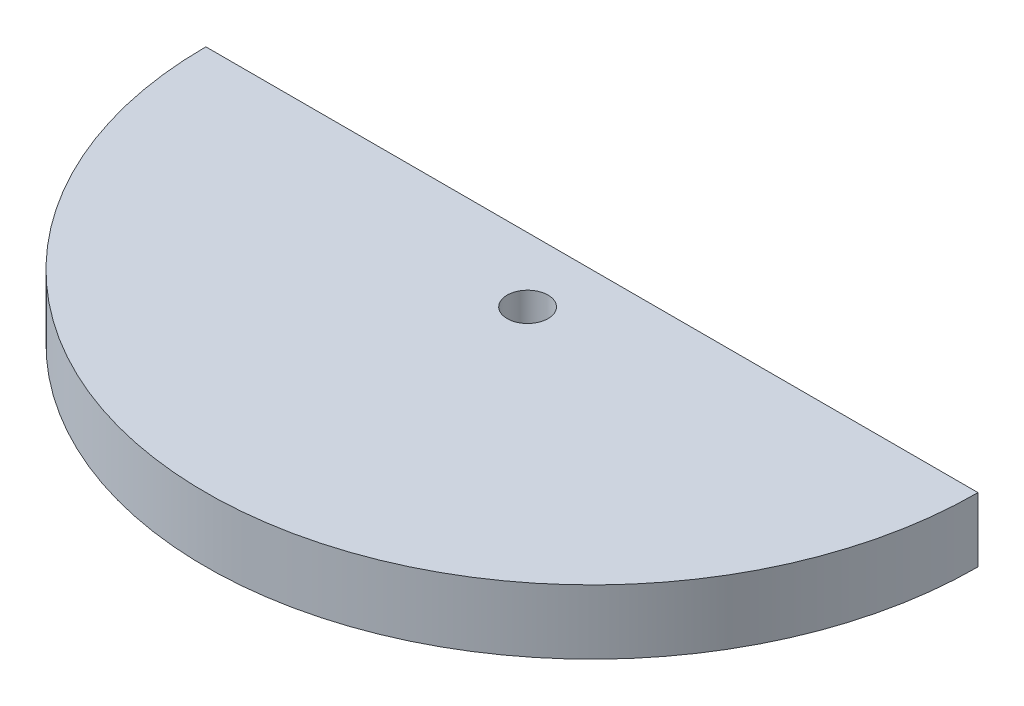
SolidWorks part; units mm, degrees
material "Pino"
ref_plane "Alzado" through (0, 0, 0) normal (0, 0, 1) x (1, 0, 0)
ref_plane "Planta" through (0, 0, 0) normal (0, 1, 0) x (1, 0, 0)
ref_plane "Vista lateral" through (0, 0, 0) normal (1, 0, 0) x (0, 0, -1)
sketch "Croquis1" plane through (0, 0, 0) normal (0, 1, 0) x (1, 0, 0)
  line L0 (-30, 0) -> (30, 0)
  line L1 (0, -5) -> (0, 0) construction
  arc A0 (-30, 0) -> (30, 0) centre (0, 0) ccw
  circle A1 centre (0, -5) radius 1.5875
  dimension "D2" = 3.175
  dimension "D1" = 60
  dimension "D3" = 5
extrude "Saliente-Extruir1" add sketch "Croquis1" along normal blind 5
